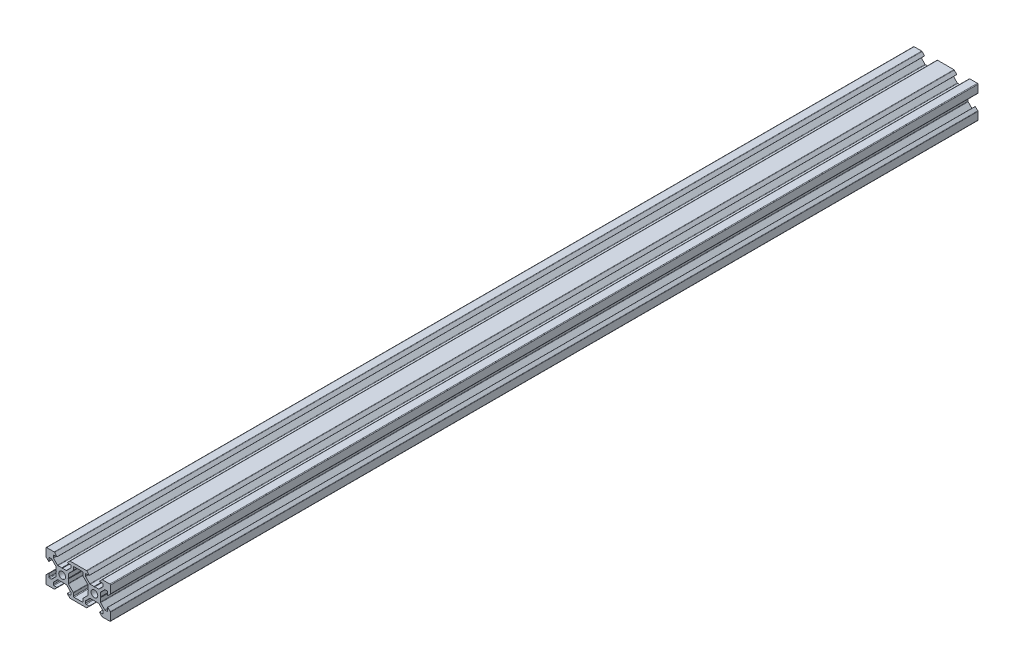
SolidWorks part; units mm, degrees
material "6063-T5"
ref_plane "前视基准面" through (0, 0, 0) normal (0, 0, 1) x (1, 0, 0)
ref_plane "上视基准面" through (0, 0, 0) normal (0, 1, 0) x (1, 0, 0)
ref_plane "右视基准面" through (0, 0, 0) normal (1, 0, 0) x (0, 0, -1)
sketch "草图1" plane through (0, 0, 0) normal (0, 0, 1) x (1, 0, 0)
  line L0 (0, 0) -> (13486.7145, 0) construction
  line L1 (0, 0) -> (0, 13486.7145) construction
  line L2 (0, 0) -> (9536.5473, 9536.5473) construction
  line L3 (0.2, 3.8) -> (2.5737, 3.8)
  line L4 (2.8565, 3.9172) -> (5.3828, 6.4435)
  line L5 (5.5, 6.7263) -> (5.5, 7.8)
  line L6 (5.1, 8.2) -> (3.2, 8.2)
  line L7 (3.1681, 8.2732) -> (4.6563, 9.8725)
  line L8 (4.9492, 10) -> (10, 10)
  line L9 (3.8, 0.2) -> (3.8, 2.5737)
  line L10 (3.9172, 2.8565) -> (6.8753, 5.8146)
  line L11 (10, 5.4182) -> (10, 50005.4182) construction
  line L12 (28.2, -3.2) -> (28.2732, -3.1681)
  line L13 (23.2, -8.2) -> (23.1681, -8.2732)
  line L14 (16.8, -8.2) -> (16.8319, -8.2732)
  line L15 (3.8, -0.2) -> (3.8, -2.5737)
  line L16 (3.9172, -2.8565) -> (6.8753, -5.8146)
  line L17 (28.2, 3.2) -> (28.2732, 3.1681)
  line L18 (16.8, 8.2) -> (16.8319, 8.2732)
  line L19 (23.2, 8.2) -> (23.1681, 8.2732)
  line L20 (20.2, 3.8) -> (22.5737, 3.8)
  line L21 (4.9492, -10) -> (10, -10)
  line L22 (3.1681, -8.2732) -> (4.6563, -9.8725)
  line L23 (5.1, -8.2) -> (3.2, -8.2)
  line L24 (5.5, -6.7263) -> (5.5, -7.8)
  line L25 (2.8565, -3.9172) -> (5.3828, -6.4435)
  line L26 (0.2, -3.8) -> (2.5737, -3.8)
  line L27 (-0.2, -3.8) -> (-2.5737, -3.8)
  line L28 (-2.8565, -3.9172) -> (-5.3828, -6.4435)
  line L29 (-5.5, -6.7263) -> (-5.5, -7.8)
  line L30 (-5.1, -8.2) -> (-3.2, -8.2)
  line L31 (-3.1681, -8.2732) -> (-4.6563, -9.8725)
  line L32 (-4.9492, -10) -> (-9.6, -10)
  line L33 (-10, -4.9492) -> (-10, -9.6)
  line L34 (-8.2732, -3.1681) -> (-9.8725, -4.6563)
  line L35 (-8.2, -5.1) -> (-8.2, -3.2)
  line L36 (-6.7263, -5.5) -> (-7.8, -5.5)
  line L37 (-3.9172, -2.8565) -> (-6.4435, -5.3828)
  line L38 (-3.8, -0.2) -> (-3.8, -2.5737)
  line L39 (-3.8, 0.2) -> (-3.8, 2.5737)
  line L40 (-3.9172, 2.8565) -> (-6.4435, 5.3828)
  line L41 (-6.7263, 5.5) -> (-7.8, 5.5)
  line L42 (-8.2, 5.1) -> (-8.2, 3.2)
  line L43 (-8.2732, 3.1681) -> (-9.8725, 4.6563)
  line L44 (-10, 4.9492) -> (-10, 9.6)
  line L45 (-4.9492, 10) -> (-9.6, 10)
  line L46 (-3.1681, 8.2732) -> (-4.6563, 9.8725)
  line L47 (-5.1, 8.2) -> (-3.2, 8.2)
  line L48 (-5.5, 6.7263) -> (-5.5, 7.8)
  line L49 (-2.8565, 3.9172) -> (-5.3828, 6.4435)
  line L50 (-0.2, 3.8) -> (-2.5737, 3.8)
  line L51 (-3.2, 8.2) -> (-3.1681, 8.2732)
  line L52 (3.2, 8.2) -> (3.1681, 8.2732)
  line L53 (-8.2, 3.2) -> (-8.2732, 3.1681)
  line L54 (22.8565, 3.9172) -> (25.3828, 6.4435)
  line L55 (25.5, 6.7263) -> (25.5, 7.8)
  line L56 (3.2, -8.2) -> (3.1681, -8.2732)
  line L57 (-3.2, -8.2) -> (-3.1681, -8.2732)
  line L58 (-8.2, -3.2) -> (-8.2732, -3.1681)
  line L59 (8.2, -5.1) -> (8.2, -3.2) [skipped]
  line L60 (8.2732, -3.1681) -> (9.8725, -4.6563) [skipped]
  line L61 (6.7263, -5.5) -> (7.8, -5.5) [skipped]
  line L62 (10, -4.9492) -> (10, -9.6) [skipped]
  line L63 (25.1, 8.2) -> (23.2, 8.2)
  line L64 (23.1681, 8.2732) -> (24.6563, 9.8725)
  line L65 (24.9492, 10) -> (29.6, 10)
  line L66 (30, 4.9492) -> (30, 9.6)
  line L67 (28.2732, 3.1681) -> (29.8725, 4.6563)
  line L68 (28.2, 5.1) -> (28.2, 3.2)
  line L69 (26.7263, 5.5) -> (27.8, 5.5)
  line L70 (23.9172, 2.8565) -> (26.4435, 5.3828)
  line L71 (23.8, 0.2) -> (23.8, 2.5737)
  line L72 (23.8, -0.2) -> (23.8, -2.5737)
  line L73 (23.9172, -2.8565) -> (26.4435, -5.3828)
  line L74 (26.7263, -5.5) -> (27.8, -5.5)
  line L75 (28.2, -5.1) -> (28.2, -3.2)
  line L76 (28.2732, -3.1681) -> (29.8725, -4.6563)
  line L77 (30, -4.9492) -> (30, -9.6)
  line L78 (24.9492, -10) -> (29.6, -10)
  line L79 (23.1681, -8.2732) -> (24.6563, -9.8725)
  line L80 (25.1, -8.2) -> (23.2, -8.2)
  line L81 (25.5, -6.7263) -> (25.5, -7.8)
  line L82 (22.8565, -3.9172) -> (25.3828, -6.4435)
  line L83 (20.2, -3.8) -> (22.5737, -3.8)
  line L84 (19.8, -3.8) -> (17.4263, -3.8)
  line L85 (17.1435, -3.9172) -> (14.6172, -6.4435)
  line L86 (14.5, -6.7263) -> (14.5, -7.8)
  line L87 (14.9, -8.2) -> (16.8, -8.2)
  line L88 (16.8319, -8.2732) -> (15.3437, -9.8725)
  line L89 (15.0508, -10) -> (10, -10)
  line L90 (16.0828, -2.8565) -> (13.1247, -5.8146)
  line L91 (16.2, -0.2) -> (16.2, -2.5737)
  line L92 (16.0828, 2.8565) -> (13.1247, 5.8146)
  line L93 (16.2, 0.2) -> (16.2, 2.5737)
  line L94 (15.0508, 10) -> (10, 10)
  line L95 (16.8319, 8.2732) -> (15.3437, 9.8725)
  line L96 (14.9, 8.2) -> (16.8, 8.2)
  line L97 (14.5, 6.7263) -> (14.5, 7.8)
  line L98 (17.1435, 3.9172) -> (14.6172, 6.4435)
  line L99 (19.8, 3.8) -> (17.4263, 3.8)
  line L100 (7, 6.1157) -> (7, 7.7742)
  line L101 (7.4258, 8.2) -> (12.5742, 8.2)
  line L102 (13, 6.1157) -> (13, 7.7742)
  line L103 (13, -6.1157) -> (13, -7.7742)
  line L104 (7.4258, -8.2) -> (12.5742, -8.2)
  line L105 (7, -6.1157) -> (7, -7.7742)
  line L106 (-0.2, 3.8) -> (0, 3.6)
  line L107 (0, 3.6) -> (0.2, 3.8)
  line L108 (3.8, 0.2) -> (3.6, 0)
  line L109 (3.6, 0) -> (3.8, -0.2)
  line L110 (0.2, -3.8) -> (0, -3.6)
  line L111 (0, -3.6) -> (-0.2, -3.8)
  line L112 (-3.8, -0.2) -> (-3.6, 0)
  line L113 (-3.6, 0) -> (-3.8, 0.2)
  line L114 (16.4, 0) -> (16.2, -0.2)
  line L115 (16.2, 0.2) -> (16.4, 0)
  line L116 (20, 3.6) -> (19.8, 3.8)
  line L117 (20.2, 3.8) -> (20, 3.6)
  line L118 (23.6, 0) -> (23.8, 0.2)
  line L119 (23.8, -0.2) -> (23.6, 0)
  line L120 (20, -3.6) -> (20.2, -3.8)
  line L121 (19.8, -3.8) -> (20, -3.6)
  line L122 (20, 0) -> (20, 50000) construction
  arc A0 (-4.9492, 10) -> (-4.6563, 9.8725) centre (-4.9492, 9.6) cw
  arc A1 (-5.1, 8.2) -> (-5.5, 7.8) centre (-5.1, 7.8) ccw
  arc A2 (-5.5, 6.7263) -> (-5.3828, 6.4435) centre (-5.1, 6.7263) ccw
  arc A3 (-2.8565, 3.9172) -> (-2.5737, 3.8) centre (-2.5737, 4.2) ccw
  arc A4 (-10, 9.6) -> (-9.6, 10) centre (-9.6, 9.6) cw
  arc A5 (-9.8725, 4.6563) -> (-10, 4.9492) centre (-9.6, 4.9492) cw
  arc A6 (-7.8, 5.5) -> (-8.2, 5.1) centre (-7.8, 5.1) ccw
  arc A7 (-6.4435, 5.3828) -> (-6.7263, 5.5) centre (-6.7263, 5.1) ccw
  arc A8 (-3.8, 2.5737) -> (-3.9172, 2.8565) centre (-4.2, 2.5737) ccw
  arc A9 (-10, -4.9492) -> (-9.8725, -4.6563) centre (-9.6, -4.9492) cw
  arc A10 (-8.2, -5.1) -> (-7.8, -5.5) centre (-7.8, -5.1) ccw
  arc A11 (-6.7263, -5.5) -> (-6.4435, -5.3828) centre (-6.7263, -5.1) ccw
  arc A12 (-3.9172, -2.8565) -> (-3.8, -2.5737) centre (-4.2, -2.5737) ccw
  arc A13 (-9.6, -10) -> (-10, -9.6) centre (-9.6, -9.6) cw
  arc A14 (-4.6563, -9.8725) -> (-4.9492, -10) centre (-4.9492, -9.6) cw
  arc A15 (-5.5, -7.8) -> (-5.1, -8.2) centre (-5.1, -7.8) ccw
  arc A16 (-5.3828, -6.4435) -> (-5.5, -6.7263) centre (-5.1, -6.7263) ccw
  arc A17 (-2.5737, -3.8) -> (-2.8565, -3.9172) centre (-2.5737, -4.2) ccw
  arc A18 (4.9492, -10) -> (4.6563, -9.8725) centre (4.9492, -9.6) cw
  arc A19 (5.1, -8.2) -> (5.5, -7.8) centre (5.1, -7.8) ccw
  arc A20 (5.5, -6.7263) -> (5.3828, -6.4435) centre (5.1, -6.7263) ccw
  arc A21 (2.8565, -3.9172) -> (2.5737, -3.8) centre (2.5737, -4.2) ccw
  arc A22 (17.4263, 3.8) -> (17.1435, 3.9172) centre (17.4263, 4.2) cw
  arc A23 (14.6172, 6.4435) -> (14.5, 6.7263) centre (14.9, 6.7263) cw
  arc A24 (14.5, 7.8) -> (14.9, 8.2) centre (14.9, 7.8) cw
  arc A25 (15.3437, 9.8725) -> (15.0508, 10) centre (15.0508, 9.6) ccw
  arc A26 (3.8, -2.5737) -> (3.9172, -2.8565) centre (4.2, -2.5737) ccw
  arc A27 (16.2, 2.5737) -> (16.0828, 2.8565) centre (15.8, 2.5737) ccw
  arc A28 (16.2, -2.5737) -> (16.0828, -2.8565) centre (15.8, -2.5737) cw
  arc A29 (17.1435, -3.9172) -> (17.4263, -3.8) centre (17.4263, -4.2) cw
  arc A30 (3.8, 2.5737) -> (3.9172, 2.8565) centre (4.2, 2.5737) cw
  arc A31 (14.5, -6.7263) -> (14.6172, -6.4435) centre (14.9, -6.7263) cw
  arc A32 (4.6563, 9.8725) -> (4.9492, 10) centre (4.9492, 9.6) cw
  arc A33 (5.5, 7.8) -> (5.1, 8.2) centre (5.1, 7.8) ccw
  arc A34 (5.3828, 6.4435) -> (5.5, 6.7263) centre (5.1, 6.7263) ccw
  arc A35 (2.5737, 3.8) -> (2.8565, 3.9172) centre (2.5737, 4.2) ccw
  arc A36 (14.9, -8.2) -> (14.5, -7.8) centre (14.9, -7.8) cw
  arc A37 (15.0508, -10) -> (15.3437, -9.8725) centre (15.0508, -9.6) ccw
  arc A38 (22.5737, -3.8) -> (22.8565, -3.9172) centre (22.5737, -4.2) cw
  arc A39 (25.3828, -6.4435) -> (25.5, -6.7263) centre (25.1, -6.7263) cw
  arc A40 (25.5, -7.8) -> (25.1, -8.2) centre (25.1, -7.8) cw
  arc A41 (24.6563, -9.8725) -> (24.9492, -10) centre (24.9492, -9.6) ccw
  arc A42 (29.6, -10) -> (30, -9.6) centre (29.6, -9.6) ccw
  arc A43 (23.9172, -2.8565) -> (23.8, -2.5737) centre (24.2, -2.5737) cw
  arc A44 (26.7263, -5.5) -> (26.4435, -5.3828) centre (26.7263, -5.1) cw
  arc A45 (28.2, -5.1) -> (27.8, -5.5) centre (27.8, -5.1) cw
  arc A46 (30, -4.9492) -> (29.8725, -4.6563) centre (29.6, -4.9492) ccw
  arc A47 (23.8, 2.5737) -> (23.9172, 2.8565) centre (24.2, 2.5737) cw
  arc A48 (26.4435, 5.3828) -> (26.7263, 5.5) centre (26.7263, 5.1) cw
  arc A49 (27.8, 5.5) -> (28.2, 5.1) centre (27.8, 5.1) cw
  arc A50 (29.8725, 4.6563) -> (30, 4.9492) centre (29.6, 4.9492) ccw
  arc A51 (30, 9.6) -> (29.6, 10) centre (29.6, 9.6) ccw
  arc A52 (22.8565, 3.9172) -> (22.5737, 3.8) centre (22.5737, 4.2) cw
  arc A53 (25.5, 6.7263) -> (25.3828, 6.4435) centre (25.1, 6.7263) cw
  arc A54 (25.1, 8.2) -> (25.5, 7.8) centre (25.1, 7.8) cw
  arc A55 (24.9492, 10) -> (24.6563, 9.8725) centre (24.9492, 9.6) ccw
  arc A56 (13.1247, 5.8146) -> (13, 6.1157) centre (13.4258, 6.1157) cw
  arc A57 (13, 7.7742) -> (12.5742, 8.2) centre (12.5742, 7.7742) ccw
  arc A58 (7, 7.7742) -> (7.4258, 8.2) centre (7.4258, 7.7742) cw
  arc A59 (6.8753, 5.8146) -> (7, 6.1157) centre (6.5742, 6.1157) ccw
  arc A60 (13, -6.1157) -> (13.1247, -5.8146) centre (13.4258, -6.1157) cw
  arc A61 (13, -7.7742) -> (12.5742, -8.2) centre (12.5742, -7.7742) cw
  arc A62 (7.4258, -8.2) -> (7, -7.7742) centre (7.4258, -7.7742) cw
  arc A63 (6.8753, -5.8146) -> (7, -6.1157) centre (6.5742, -6.1157) cw
  circle A64 centre (0, 0) radius 2
  circle A65 centre (20, 0) radius 2
  point P12 (3.1, 8.2)
  point P34 (3.1, -8.2)
  point P41 (-3.1, -8.2)
  point P47 (-8.2, -3.1)
  point P54 (-8.2, 3.1)
  point P60 (-3.1, 8.2)
  point P62 (0, 0)
  point P118 (6.5607, 5.5)
  point P121 (3.8, 2.7393)
  point P124 (10, 10)
  point P127 (4.775, 10)
  point P130 (5.5, 8.2)
  point P133 (5.5, 6.5607)
  point P136 (2.7393, 3.8)
  point P239 (17.2607, 3.8)
  point P240 (14.5, 6.5607)
  point P241 (14.5, 8.2)
  point P242 (15.225, 10)
  point P243 (16.2, 2.7393)
  point P244 (13.4393, 5.5)
  point P245 (20, 0)
  point P246 (23.1, 8.2)
  point P247 (28.2, 3.1)
  point P248 (28.2, -3.1)
  point P249 (23.1, -8.2)
  point P250 (16.9, -8.2)
  point P251 (16.9, 8.2)
  point P253 (10, 8.2)
  point P257 (13, 5.9393)
  point P260 (13, 8.2)
  point P263 (7, 8.2)
  point P266 (7, 5.9393)
  point P269 (13, -5.9393)
  point P272 (13, -8.2)
  point P275 (7, -8.2)
  point P278 (7, -5.9393)
  point P297 (0, 0)
  point P306 (20, 0)
  dimension "D9" = 0.4
  dimension "D13" = 0.4258
  dimension "D14" = 4
  dimension "D3" = 3.1
  dimension "D4" = 1.5
  dimension "D5" = 1.8
  dimension "D6" = 4.775
  dimension "D7" = 20
  dimension "D10" = 10
  dimension "D11" = 10
  dimension "D12" = 1.5
  dimension "D18" = 10
  dimension "D19" = 10
  dimension "D23" = 45
  dimension "D25" = 5.5
  dimension "D26" = 1.8
  dimension "D27" = 1.8
  dimension "D28" = 10
  dimension "D30" = 7.6
  dimension "D31" = 3.8
  dimension "D32" = 3.8
  dimension "D33" = 3.8
  dimension "D34" = 10
  dimension "D35" = 0.4
  dimension "D8" = 4
  dimension "D24" = 4
  dimension "D29" = 4
extrude "凸台-拉伸1" add sketch "草图1" along normal blind 538
hole_wizard "M5 螺纹孔1" positions "草图4" profile "草图3" tap size "M5" standard "GB"
sketch "草图4" plane through (0, 0, 0) normal (0, 0, -1) x (-1, 0, 0)
  point P0 (0, 0)
  point P3 (-20, 0)
  point P6 (-618.6657, 229.3379)
  point P8 (-600.3191, 227.0345)
sketch "草图3" plane through (0, 0, 0) normal (1, 0, 0) x (0, 1, 0)
  line L0 (0, 0) -> (0, 16.2618)
  line L1 (0, 16.2618) -> (2.1, 15)
  line L2 (2.1, 15) -> (2.1, 0)
  line L5 (2.1, 0) -> (0, 0)
  line L10 (0, 16.2618) -> (-2.1, 15) construction
  line L11 (0, -6.35) -> (0, 107.95) construction
  dimension "螺纹孔钻头直径" = 4.2
  dimension "螺纹孔钻头深度" = 15
  dimension "导头角度" = 118
cosmetic thread "孔螺蚊线1" parameters "D1"=15, "D2"=5
cosmetic thread "孔螺蚊线2" parameters "D1"=15, "D2"=5
hole_wizard "M5 螺纹孔2" positions "草图6" profile "草图5" tap size "M5" standard "GB"
sketch "草图6" plane through (0, 0, 538) normal (0, 0, 1) x (1, 0, 0)
  point P0 (0, 0)
  point P3 (20, 0)
sketch "草图5" plane through (0, 0, 538) normal (1, 0, 0) x (0, -1, 0)
  line L0 (0, 0) -> (0, 16.2618)
  line L1 (0, 16.2618) -> (2.1, 15)
  line L2 (2.1, 15) -> (2.1, 0)
  line L5 (2.1, 0) -> (0, 0)
  line L10 (0, 16.2618) -> (-2.1, 15) construction
  line L11 (0, -6.35) -> (0, 107.95) construction
  dimension "螺纹孔钻头直径" = 4.2
  dimension "螺纹孔钻头深度" = 15
  dimension "导头角度" = 118
cosmetic thread "孔螺蚊线3" parameters "D1"=15, "D2"=5
cosmetic thread "孔螺蚊线4" parameters "D1"=15, "D2"=5
hole_wizard "M4 螺纹孔1" [suppressed] positions "草图7" profile "草图8" tap size "M4" standard "GB"
sketch "草图7" plane through (0, -3.8, 0) normal (0, -1, 0) x (-1, 0, 0)
  line L0 (-20, -538) -> (-20, 0) construction
  line L1 (0, -538) -> (0, 0) construction
  line L2 (9.6, 0) -> (4.9492, 0) construction
  point P0 (0, -42.25)
  point P2 (-20, -42.25)
  dimension "D1" = 42.25
cosmetic thread "孔螺蚊线7" [suppressed] parameters "D2"=4
sketch "草图8" plane through (0, -3.8, 42.25) normal (1, 0, 0) x (0, 0, -1)
  line L0 (0, 0) -> (0, 13.8)
  line L1 (0, 13.8) -> (1.65, 13.8)
  line L2 (1.65, 13.8) -> (1.65, 0)
  line L5 (1.65, 0) -> (0, 0)
  line L11 (0, -6.35) -> (0, 107.95) construction
  dimension "通孔螺纹孔钻头直径" = 3.3
  dimension "通孔螺纹孔钻头深度" = 13.8
cosmetic thread "孔螺蚊线8" [suppressed] parameters "D2"=4
